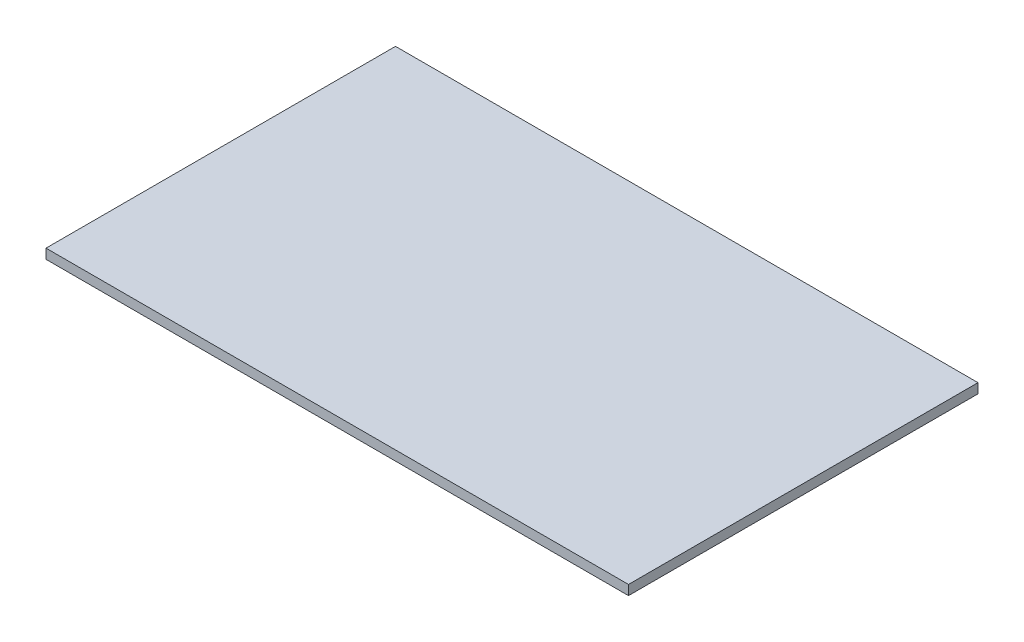
SolidWorks part; units mm, degrees
ref_plane "Спереди" through (0, 0, 0) normal (0, 0, 1) x (1, 0, 0)
ref_plane "Сверху" through (0, 0, 0) normal (0, 1, 0) x (1, 0, 0)
ref_plane "Справа" through (0, 0, 0) normal (1, 0, 0) x (0, 0, -1)
sketch "Эскиз1" plane through (0, 0, 0) normal (0, 1, 0) x (1, 0, 0)
  line L1 (-300, 180) -> (300, 180)
  line L2 (-300, 180) -> (-300, -180)
  line L3 (-300, -180) -> (300, -180)
  line L4 (300, 180) -> (300, -180)
  line L5 (-300, 180) -> (300, -180) construction
  line L6 (-300, -180) -> (300, 180) construction
  point P0 (0, 0)
extrude "Бобышка-Вытянуть1" add sketch "Эскиз1" along normal blind 10
